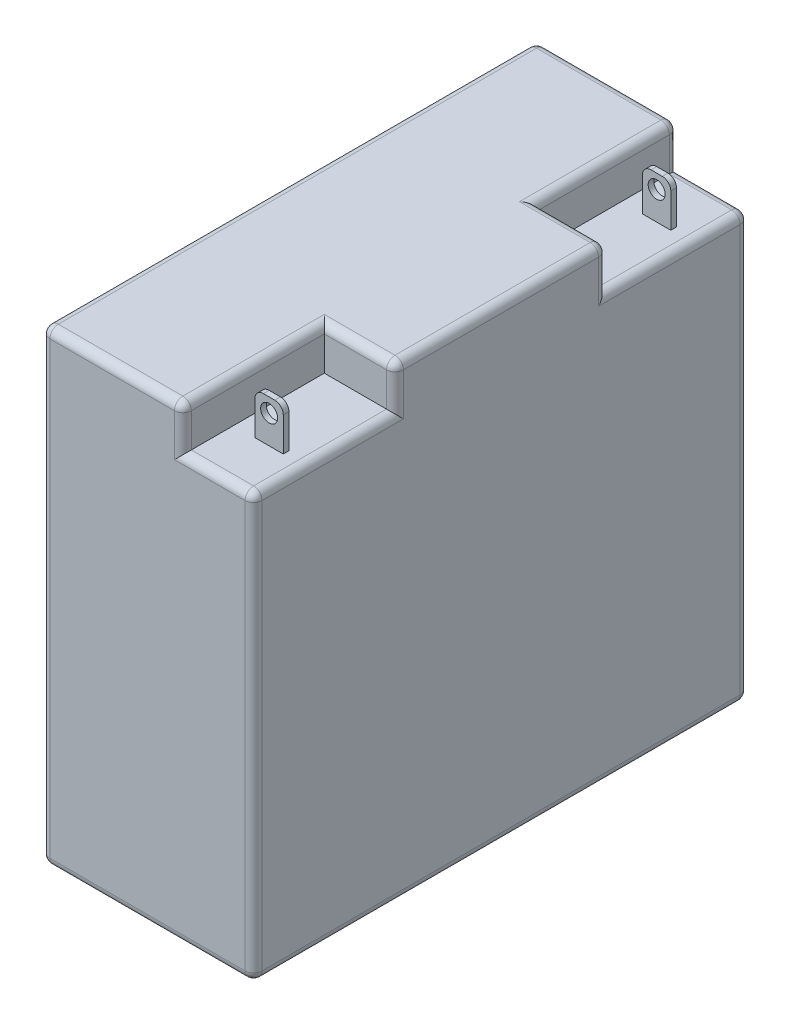
SolidWorks part; units mm, degrees
ref_plane "Спереди" through (0, 0, 0) normal (0, 0, 1) x (1, 0, 0)
ref_plane "Сверху" through (0, 0, 0) normal (0, 1, 0) x (1, 0, 0)
ref_plane "Справа" through (0, 0, 0) normal (1, 0, 0) x (0, 0, -1)
sketch "Эскиз1" plane through (0, 0, 0) normal (0, 1, 0) x (1, 0, 0)
  line L1 (0, 0) -> (75, 0)
  line L2 (0, 0) -> (0, 175)
  line L3 (0, 175) -> (75, 175)
  line L4 (75, 0) -> (75, 175)
  dimension "D1" = 75
  dimension "D2" = 175
extrude "Бобышка-Вытянуть1" add sketch "Эскиз1" along normal blind 165
sketch "Эскиз2" plane through (0, 165, 0) normal (0, 1, 0) x (1, 0, 0)
  line L1 (75, 175) -> (50, 175)
  line L2 (75, 175) -> (75, 125)
  line L3 (75, 125) -> (50, 125)
  line L4 (50, 175) -> (50, 125)
  line L5 (75, 0) -> (50, 0)
  line L6 (75, 0) -> (75, 50)
  line L7 (75, 50) -> (50, 50)
  line L8 (50, 0) -> (50, 50)
  dimension "D1" = 25
  dimension "D2" = 50
extrude "Вырез-Вытянуть1" cut sketch "Эскиз2" against normal blind 15
sketch "Эскиз3" plane through (0, 150, 0) normal (0, 1, 0) x (1, 0, 0)
  line L0 (75, 175) -> (50, 175) construction
  line L1 (57.5, 157) -> (67.5, 157)
  line L2 (57.5, 157) -> (57.5, 155)
  line L3 (57.5, 155) -> (67.5, 155)
  line L4 (67.5, 157) -> (67.5, 155)
  line L5 (62.5, -825) -> (62.5, 49175) construction
  line L6 (-925, 87.5) -> (49075, 87.5) construction
  line L7 (75, 50) -> (75, 125) construction
  line L8 (57.5, 20) -> (67.5, 20)
  line L9 (67.5, 18) -> (67.5, 20)
  line L10 (57.5, 18) -> (67.5, 18)
  line L11 (57.5, 18) -> (57.5, 20)
  point P9 (62.5, 175)
  point P10 (62.5, 157)
  point P14 (75, 87.5)
  dimension "D1" = 10
  dimension "D2" = 20
  dimension "D3" = 2
extrude "Бобышка-Вытянуть2" add sketch "Эскиз3" along normal blind 15 separate body
sketch "Эскиз4" plane through (0, 0, -18) normal (0, 0, 1) x (1, 0, 0)
  line L0 (62.5, 165) -> (62.5, 150) construction
  line L1 (57.5, 165) -> (67.5, 165) construction
  line L2 (57.5, 150) -> (67.5, 150) construction
  circle A0 centre (62.5, 160) radius 3
  dimension "D1" = 6
  dimension "D2" = 5
extrude "Вырез-Вытянуть3" cut sketch "Эскиз4" against normal blind 200
fillet "Скругление1" radius 3 2 edges at (67.5, 165, -19) (57.5, 165, -19)
fillet "Скругление2" radius 3 2 edges at (67.5, 165, -156) (57.5, 165, -156)
fillet "Скругление3" radius 3 24 edges at (0, 0, -87.5) (0, 82.5, -175) (37.5, 0, -175) (62.5, 150, -175) (50, 157.5, -175) (75, 75, -175) (75, 0, -87.5) (75, 150, -25) (75, 157.5, -50) (75, 157.5, -125) (75, 150, -150) (62.5, 165, -50) (50, 165, -25) (0, 165, -87.5) (25, 165, -175) (50, 165, -150) (62.5, 165, -125) (75, 165, -87.5) (75, 75, 0) (37.5, 0, 0) (0, 82.5, 0) (25, 165, 0) (50, 157.5, 0) (62.5, 150, 0)
